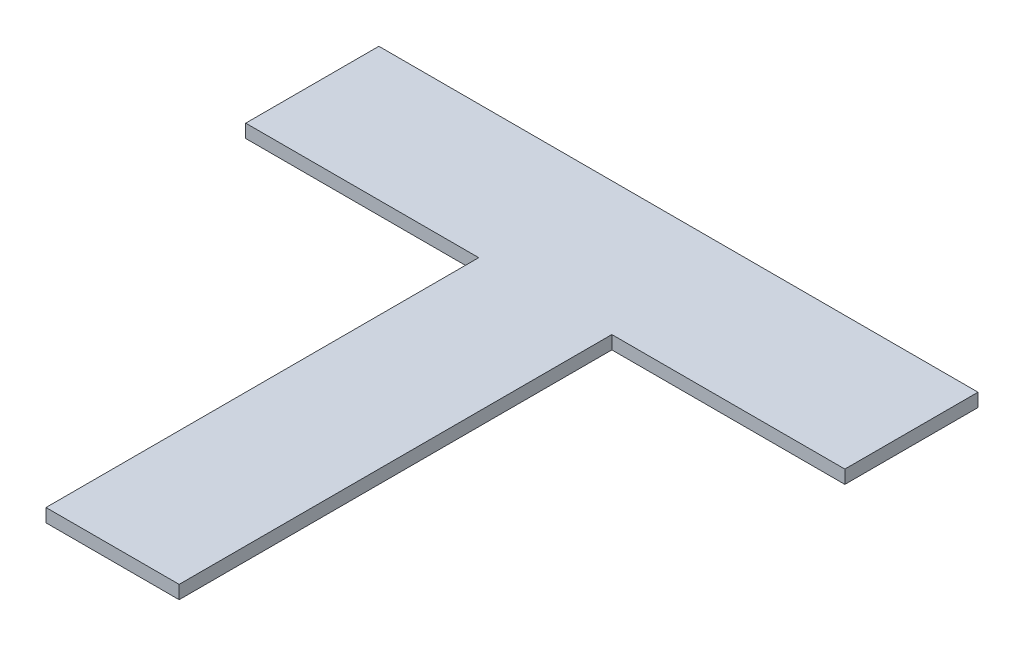
SolidWorks part; units mm, degrees
ref_plane "Plan de face" through (0, 0, 0) normal (0, 0, 1) x (1, 0, 0)
ref_plane "Plan de dessus" through (0, 0, 0) normal (0, 1, 0) x (1, 0, 0)
ref_plane "Plan de droite" through (0, 0, 0) normal (1, 0, 0) x (0, 0, -1)
sketch "Esquisse1" plane through (0, 0, 0) normal (0, 1, 0) x (1, 0, 0)
  line L1 (-10, 22.5) -> (10, 22.5)
  line L2 (-10, 22.5) -> (-10, -42.5)
  line L3 (-10, -42.5) -> (10, -42.5)
  line L4 (10, 22.5) -> (10, -42.5)
  dimension "D1" = 20
  dimension "D2" = 65
  dimension "D3" = 10
  dimension "D4" = 22.5
extrude "Boss.-Extru.1" add sketch "Esquisse1" along normal blind 2
sketch "Esquisse2" plane through (0, 0, -22.5) normal (0, 0, -1) x (-1, 0, 0)
  line L1 (-45, 2) -> (45, 2)
  line L2 (-45, 2) -> (-45, 0)
  line L3 (-45, 0) -> (45, 0)
  line L4 (45, 2) -> (45, 0)
  dimension "D1" = 2
  dimension "D2" = 90
  dimension "D3" = 45
extrude "Boss.-Extru.2" add sketch "Esquisse2" along normal blind 20
